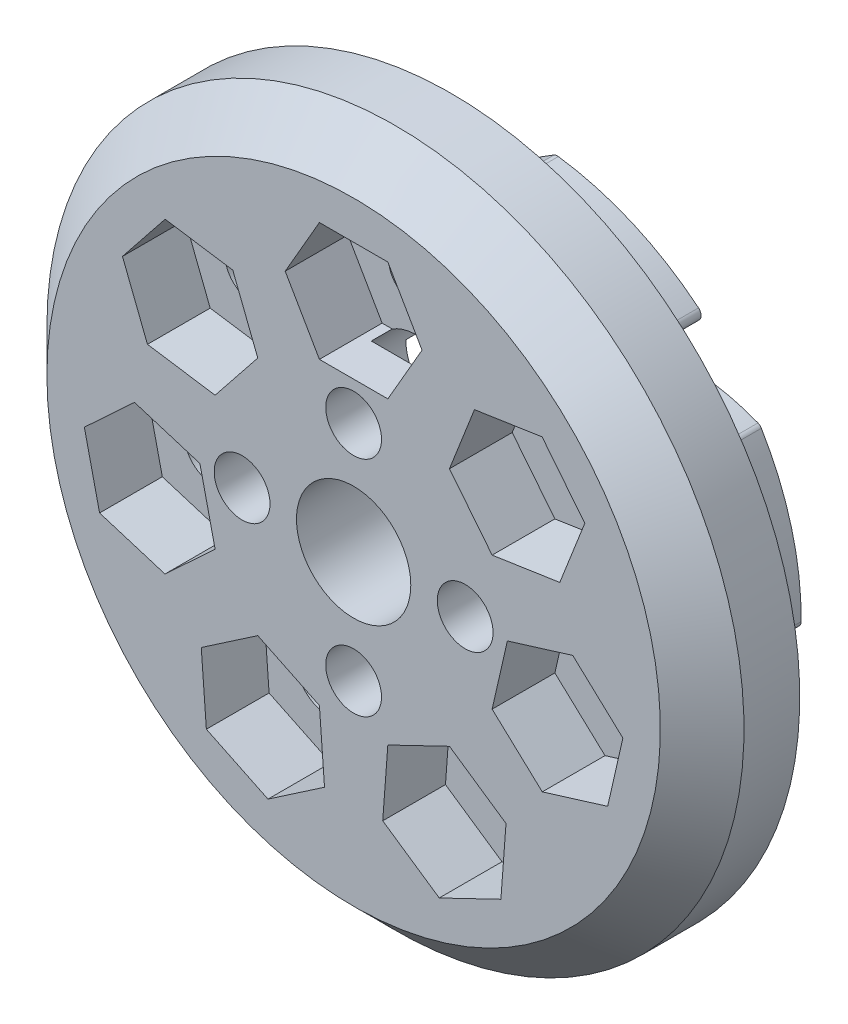
SolidWorks part; units mm, degrees
material "ABS"
ref_plane "Front Plane" through (0, 0, 0) normal (0, 0, 1) x (1, 0, 0)
ref_plane "Top Plane" through (0, 0, 0) normal (0, 1, 0) x (1, 0, 0)
ref_plane "Right Plane" through (0, 0, 0) normal (1, 0, 0) x (0, 0, -1)
sketch "Sketch1" plane through (0, 0, 0) normal (0, 1, 0) x (1, 0, 0)
  line L0 (0, -2) -> (0, -9)
  line L1 (0, -9) -> (25, -9)
  line L2 (25, -9) -> (25, -2)
  line L3 (25, -2) -> (22.3599, -2)
  line L4 (22.3599, -2) -> (19.8, 0)
  line L5 (19.8, 0) -> (8.7, 0)
  line L6 (8.7, 0) -> (8.7, -2)
  line L7 (8.7, -2) -> (0, -2)
  dimension "D1" = 2
  dimension "D2" = 8.7
  dimension "D3" = 7
  dimension "D4" = 25
  dimension "D5" = 19.8
  dimension "D6" = 142
revolve "Revolve1" add sketch "Sketch1" angle 360 about L0
sketch "Sketch5" plane through (0, 0, 0) normal (0, 0, 1) x (-1, 0, 0)
  arc A5 (3.3645, -7.9146) -> (2.5843, -15.6797) centre (-4.1574, -11.0806) cw
  arc A6 (2.5843, -15.6797) -> (-2.457, -20.2488) centre (-9.4435, -7.4745) cw
  arc A7 (-2.457, -20.2488) -> (-15.3256, -13.4601) centre (0, 0) cw
  arc A8 (1.9404, -8.3782) -> (-15.3256, -13.4601) centre (-9.7757, -0.4439) cw
  arc A11 (3.3645, -7.9146) -> (1.9404, -8.3782) centre (0, 0) cw
  arc A12 (1.9392, -16.5535) -> (-1.177, -17.2083) centre (-0.0152, -14.9946) cw construction
  arc A13 (-1.177, -17.2083) -> (-6.1928, -19.4344) centre (-2.8034, -20.3074) ccw construction
  point P30 (0, 0)
sketch "Sketch6" plane through (0, 0, 0) normal (0, 0, -1) x (-1, 0, 0)
  arc A21 (-12.3329, 14.6658) -> (-12.7383, 15.5447) centre (-12.4214, 15.1579) cw
  arc A22 (2.0184, 8.7925) -> (2.2975, 8.5984) centre (2.4265, 9.0814) ccw
  arc A23 (2.7337, 8.4698) -> (3.3657, 8.8006) centre (2.8872, 8.9456) ccw
  arc A24 (2.1228, 8.6431) -> (-14.2323, 14.1895) centre (-9.7757, 0.4439) ccw
  arc A25 (3.1976, 8.3057) -> (2.1228, 8.6431) centre (0, 0) ccw
  arc A26 (3.1976, 8.3057) -> (2.3365, 15.5107) centre (-4.1574, 11.0806) ccw
  arc A27 (2.3365, 15.5107) -> (-2.5166, 19.9391) centre (-9.4435, 7.4745) ccw
  arc A28 (-2.5166, 19.9391) -> (-14.2323, 14.1895) centre (0, 0) ccw
  arc A29 (2.0184, 8.7925) -> (-12.3329, 14.6658) centre (-9.7757, 0.4439) ccw
  arc A30 (2.7337, 8.4698) -> (2.2975, 8.5984) centre (0, 0) ccw
  arc A31 (3.3657, 8.8006) -> (2.3365, 15.5107) centre (-4.1574, 11.0806) ccw
  arc A32 (2.3365, 15.5107) -> (-2.369, 19.8559) centre (-9.4435, 7.4745) ccw
  arc A33 (-2.6838, 19.9173) -> (-12.7383, 15.5447) centre (0, 0) ccw
  arc A34 (-2.369, 19.8559) -> (-2.6838, 19.9173) centre (-2.617, 19.4217) ccw
  dimension "D2" = 0.5
  dimension "D3" = 0.5
  dimension "D1" = 0.3
extrude "Boss-Extrude1" add sketch "Sketch6" along normal blind 3 and the other way blind 1
pattern_circular "CirPattern1" count 7 over 360 about axis through (0, 0, 0) along (0, 0, 1) of "Boss-Extrude1"
sketch "Sketch2" plane through (0, 0, 9) normal (0, 0, 1) x (1, 0, 0)
  line L0 (0, 0) -> (0, 8) construction
  circle A0 centre (0, 0) radius 4.1
  circle A1 centre (0, 8) radius 2
  circle A2 centre (8, 0) radius 2
  circle A3 centre (0, -8) radius 2
  circle A4 centre (-8, 0) radius 2
  point P14 (0, 0)
  dimension "D1" = 4
  dimension "D3" = 8.2
  dimension "D2" = 8
  dimension "D4" = 4
extrude "Cut-Extrude1" cut sketch "Sketch2" against normal through all
sketch "Sketch3" plane through (0, 0, 9) normal (0, 0, 1) x (1, 0, 0)
  line L0 (0, 0) -> (0, 15) construction
  circle A0 centre (0, 15) radius 2
  circle A1 centre (11.7275, 9.3523) radius 2
  circle A2 centre (14.6239, -3.3378) radius 2
  circle A3 centre (6.5083, -13.5145) radius 2
  circle A4 centre (-6.5083, -13.5145) radius 2
  circle A5 centre (-14.6239, -3.3378) radius 2
  circle A6 centre (-11.7275, 9.3523) radius 2
  point P18 (0, 0)
  dimension "D2" = 4
  dimension "D1" = 15
  dimension "D3" = 7
extrude "Cut-Extrude2" cut sketch "Sketch3" against normal through all
sketch "Sketch4" plane through (0, 0, 9) normal (0, 0, 1) x (1, 0, 0)
  line L0 (8.6677, 13.1892) -> (6.8748, 8.6209)
  line L1 (2.4537, 19.25) -> (-2.4537, 19.25)
  line L2 (-2.4537, 19.25) -> (-4.9075, 15)
  line L3 (-4.9075, 15) -> (-2.4537, 10.75)
  line L4 (-2.4537, 10.75) -> (2.4537, 10.75)
  line L5 (2.4537, 10.75) -> (4.9075, 15)
  line L6 (4.9075, 15) -> (2.4537, 19.25)
  line L7 (6.8748, 8.6209) -> (9.9346, 4.7841)
  line L8 (9.9346, 4.7841) -> (14.7872, 5.5155)
  line L9 (14.7872, 5.5155) -> (16.5801, 10.0838)
  line L10 (16.5801, 10.0838) -> (13.5204, 13.9206)
  line L11 (13.5204, 13.9206) -> (8.6677, 13.1892)
  line L12 (15.7159, 1.4466) -> (11.0265, 0.0001)
  line L13 (11.0265, 0.0001) -> (9.9345, -4.7843)
  line L14 (9.9345, -4.7843) -> (13.5319, -8.1223)
  line L15 (13.5319, -8.1223) -> (18.2214, -6.6757)
  line L16 (18.2214, -6.6757) -> (19.3134, -1.8913)
  line L17 (19.3134, -1.8913) -> (15.7159, 1.4466)
  line L18 (10.9297, -11.3853) -> (6.875, -8.6208)
  line L19 (6.875, -8.6208) -> (2.4535, -10.7501)
  line L20 (2.4535, -10.7501) -> (2.0868, -15.6438)
  line L21 (2.0868, -15.6438) -> (6.1415, -18.4083)
  line L22 (6.1415, -18.4083) -> (10.563, -16.279)
  line L23 (10.563, -16.279) -> (10.9297, -11.3853)
  line L24 (-2.0868, -15.6438) -> (-2.4535, -10.7501)
  line L25 (-2.4535, -10.7501) -> (-6.875, -8.6208)
  line L26 (-6.875, -8.6208) -> (-10.9297, -11.3853)
  line L27 (-10.9297, -11.3853) -> (-10.563, -16.279)
  line L28 (-10.563, -16.279) -> (-6.1415, -18.4083)
  line L29 (-6.1415, -18.4083) -> (-2.0868, -15.6438)
  line L30 (-13.5319, -8.1223) -> (-9.9345, -4.7843)
  line L31 (-9.9345, -4.7843) -> (-11.0265, 0.0001)
  line L32 (-11.0265, 0.0001) -> (-15.7159, 1.4466)
  line L33 (-15.7159, 1.4466) -> (-19.3134, -1.8913)
  line L34 (-19.3134, -1.8913) -> (-18.2214, -6.6757)
  line L35 (-18.2214, -6.6757) -> (-13.5319, -8.1223)
  line L36 (-14.7872, 5.5155) -> (-9.9346, 4.7841)
  line L37 (-9.9346, 4.7841) -> (-6.8748, 8.6209)
  line L38 (-6.8748, 8.6209) -> (-8.6677, 13.1892)
  line L39 (-8.6677, 13.1892) -> (-13.5204, 13.9206)
  line L40 (-13.5204, 13.9206) -> (-16.5801, 10.0838)
  line L41 (-16.5801, 10.0838) -> (-14.7872, 5.5155)
  circle A0 centre (0, 15) radius 4.25 construction
  circle A1 centre (11.7275, 9.3523) radius 4.25 construction
  circle A2 centre (14.6239, -3.3378) radius 4.25 construction
  circle A3 centre (6.5083, -13.5145) radius 4.25 construction
  circle A4 centre (-6.5083, -13.5145) radius 4.25 construction
  circle A5 centre (-14.6239, -3.3378) radius 4.25 construction
  circle A6 centre (-11.7275, 9.3523) radius 4.25 construction
  point P60 (0, 0)
  dimension "D1" = 8.5
  dimension "D2" = 7
extrude "Cut-Extrude3" cut sketch "Sketch4" against normal blind 4.5
chamfer "Chamfer1" distance 3 1 edges at (-25, 0, 9)
sketch "Sketch7" plane through (0, 0, -3) normal (0, 0, -1) x (-1, 0, 0)
  circle A0 centre (0, 8) radius 3.25
  circle A1 centre (8, 0) radius 3.25
  circle A2 centre (0, -8) radius 3.25
  circle A3 centre (-8, 0) radius 3.25
  point P12 (0, 0)
  dimension "D1" = 6.5
  dimension "D2" = 4
extrude "Cut-Extrude4" cut sketch "Sketch7" against normal blind 9
